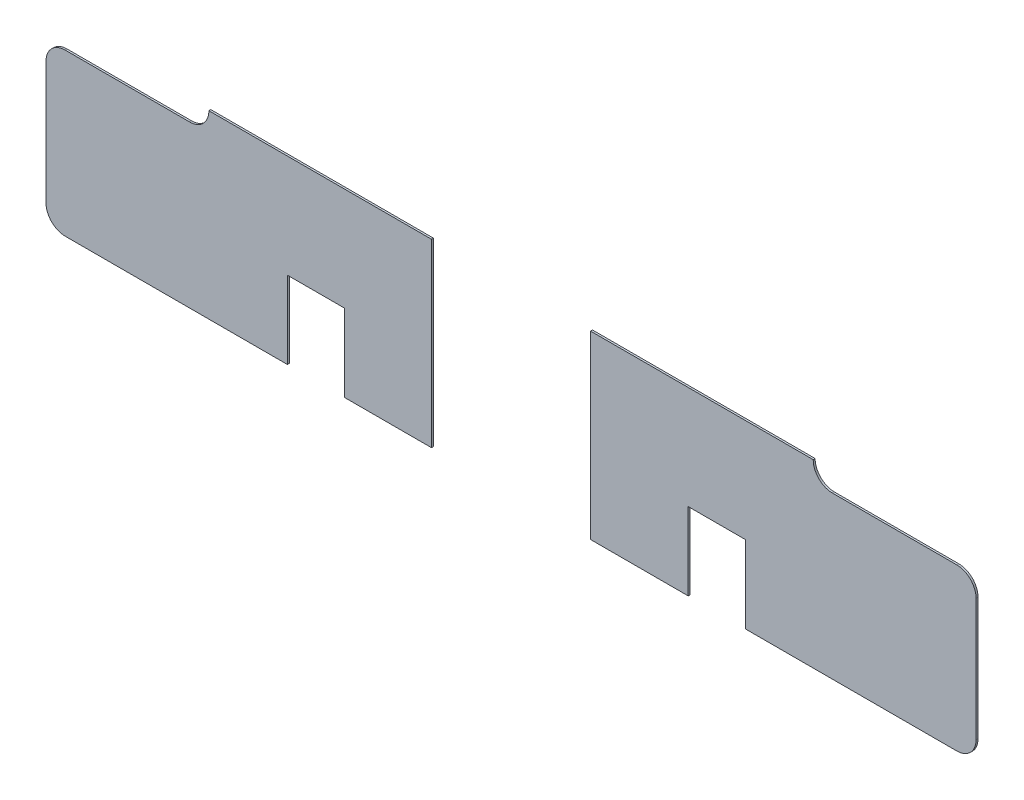
SolidWorks part; units mm, degrees
ref_plane "Alzado" through (0, 0, 0) normal (0, 0, 1) x (1, 0, 0)
ref_plane "Planta" through (0, 0, 0) normal (0, 1, 0) x (1, 0, 0)
ref_plane "Vista lateral" through (0, 0, 0) normal (1, 0, 0) x (0, 0, -1)
sketch "Model" plane through (0, 0, 0) normal (0, 0, 1) x (1, 0, 0)
  line L0 (58.3297, -1.8) -> (58.3297, 4.533)
  line L1 (50.8972, 5.533) -> (57.3431, 5.533)
  line L2 (22.7268, -2.8) -> (11.2351, -2.8)
  line L3 (22.7268, 1.2) -> (22.7268, -2.8)
  line L4 (25.6868, 1.2) -> (22.7268, 1.2)
  line L5 (25.6868, -2.8) -> (25.6868, 1.2)
  line L6 (30.1782, -2.8) -> (25.6868, -2.8)
  line L7 (30.1782, 6.533) -> (30.1782, -2.8)
  line L8 (38.4, -2.8) -> (38.4, 6.533)
  line L9 (43.4468, -2.8) -> (38.4, -2.8)
  line L10 (43.4468, 1.2) -> (43.4468, -2.8)
  line L11 (46.4068, 1.2) -> (43.4468, 1.2)
  line L12 (46.4068, -2.8) -> (46.4068, 1.2)
  line L13 (57.3431, -2.8) -> (46.4068, -2.8)
  line L14 (10.2485, -1.8133) -> (10.2485, 4.533)
  line L15 (11.2351, 5.533) -> (17.681, 5.533)
  line L16 (18.6677, 6.533) -> (30.1782, 6.533)
  line L17 (49.9105, 6.533) -> (38.4, 6.533)
  arc A0 (58.3297, 4.533) -> (57.3431, 5.533) centre (57.3364, 4.5397) ccw
  arc A1 (49.9105, 6.533) -> (50.8972, 5.533) centre (50.9038, 6.5263) ccw
  arc A2 (57.3431, -2.8) -> (58.3297, -1.8) centre (57.3364, -1.8067) ccw
  arc A3 (10.2485, -1.8) -> (11.2351, -2.8) centre (11.2418, -1.8067) ccw
  arc A4 (17.681, 5.533) -> (18.6677, 6.533) centre (17.6744, 6.5263) ccw
  arc A5 (11.2351, 5.533) -> (10.2485, 4.533) centre (11.2418, 4.5397) ccw
extrude "Saliente-Extruir1" add sketch "Model" along normal blind 0.1 contours L15 A5 L14 A3 L2 L3 L4 L5 L6 L7 L16 A4 | L13 A2 L0 A0 L1 A1 L17 L8 L9 L10 L11 L12
